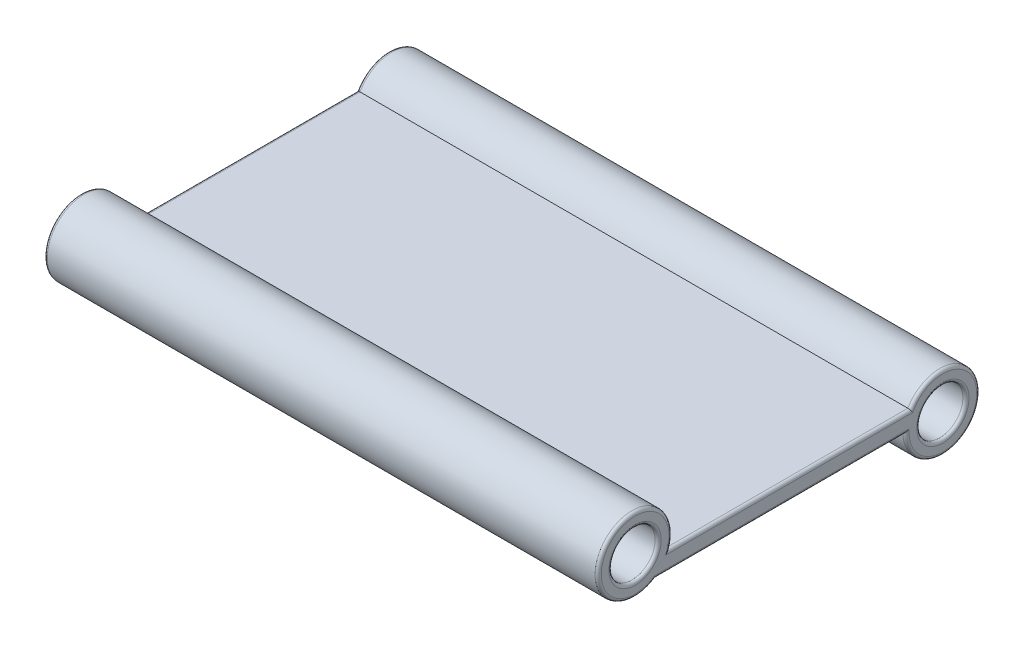
SolidWorks part; units mm, degrees
ref_plane "Front Plane" through (0, 0, 0) normal (0, 0, 1) x (1, 0, 0)
ref_plane "Top Plane" through (0, 0, 0) normal (0, 1, 0) x (1, 0, 0)
ref_plane "Right Plane" through (0, 0, 0) normal (1, 0, 0) x (0, 0, -1)
sketch "Sketch1" plane through (0, 0, 0) normal (0, 1, 0) x (1, 0, 0)
  line L0 (0, -55) -> (0, 55) construction
  line L1 (-9, 6.25) -> (9, 6.25)
  line L2 (-9, 6.25) -> (-9, -3.75)
  line L3 (-9, -3.75) -> (9, -3.75)
  line L4 (9, 6.25) -> (9, -3.75)
  line L5 (-55, 0) -> (55, 0) construction
  dimension "D1" = 18
  dimension "D2" = 9
  dimension "D3" = 10
  dimension "D4" = 6.25
extrude "Boss-Extrude1" add sketch "Sketch1" along normal blind 0.6
sketch "Sketch2" plane through (9, 0, 0) normal (1, 0, 0) x (0, 0, -1)
  line L0 (5.5, 0) -> (-5.5, 0) construction
  line L2 (6.25, 0.6) -> (6.25, 0) construction
  line L3 (-3.75, 0.6) -> (-3.75, 0) construction
  circle A0 centre (-3.75, 1) radius 1.2
  circle A1 centre (6.25, 0) radius 1.2
  dimension "D1" = 2.4
  dimension "D2" = 2.4
  dimension "D3" = 1
  dimension "D4" = 0
  dimension "D5" = 0
  dimension "D6" = 0
extrude "Boss-Extrude2" add sketch "Sketch2" against normal blind 18
sketch "Sketch3" plane through (9, 0, 0) normal (1, 0, 0) x (0, 0, -1)
  circle A0 centre (-3.75, 1) radius 0.75
  circle A1 centre (6.25, 0) radius 0.75
  dimension "D1" = 1.5
  dimension "D2" = 1.5
extrude "Cut-Extrude1" cut sketch "Sketch3" against normal blind 18
sketch "Sketch8" plane through (0, 0, 0) normal (1, 0, 0) x (0, 0, -1)
  line L2 (-4.5293, 0.6) -> (4.55, 0.6) construction
  circle A0 centre (-3.85, 1.2) radius 0.6
  dimension "D1" = 1.2
  dimension "D2" = 0.6
extrude "Cut-Extrude4" cut sketch "Sketch8" against normal mid plane 12
fillet "Fillet5" radius 0.1 12 edges at (9, 1.7381, 4.6962) (-9, 1.7381, 4.6962) (9, 0.6, -1.2961) (-9, -0.3106, -7.4091) (9, -0.3106, -7.4091) (9, 0, -0.9817) (9, 1, 3) (9, 0, -7) (-9, 0, -0.9817) (-9, 0.6, -1.2961) (-9, 1, 3) (-9, 0, -7)
